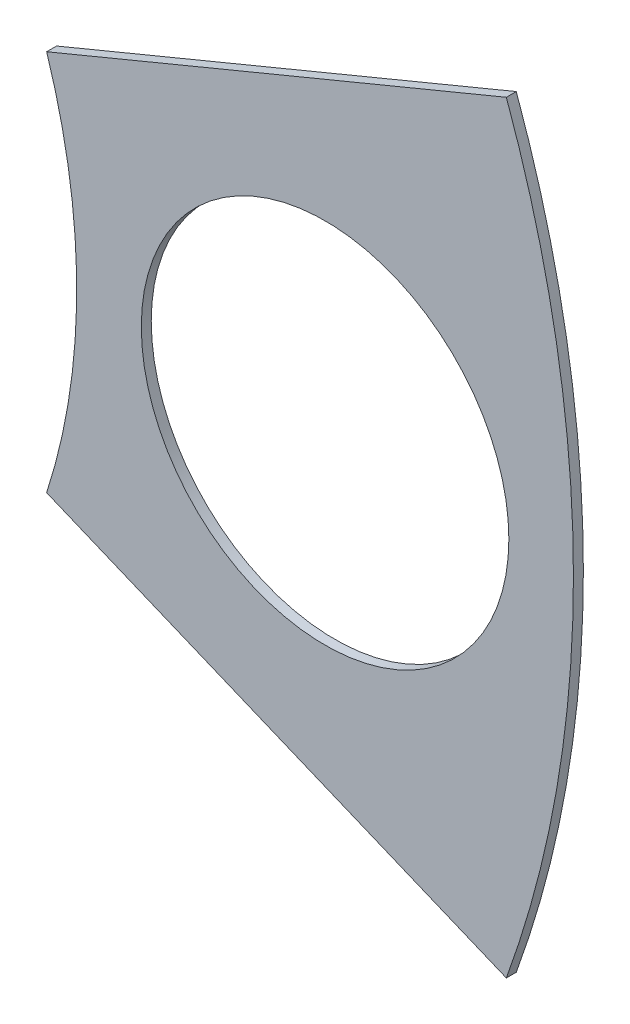
SolidWorks part; units mm, degrees
material "Copper"
ref_plane "Front Plane" through (0, 0, 0) normal (0, 0, 1) x (1, 0, 0)
ref_plane "Top Plane" through (0, 0, 0) normal (0, 1, 0) x (1, 0, 0)
ref_plane "Right Plane" through (0, 0, 0) normal (1, 0, 0) x (0, 0, -1)
sketch "Sketch4" plane through (0, 0, 0) normal (0, 0, 1) x (1, 0, 0)
  circle A0 centre (0, 0) radius 28.575
  dimension "D1" = 57.15
extrude "Boss-Extrude2" add sketch "Sketch4" along normal blind 0.254
sketch "Sketch5" plane through (0, 0, 0.254) normal (0, 0, 1) x (1, 0, 0)
  circle A0 centre (0, 0) radius 15.875
  circle A1 centre (0, 0) radius 28.575 construction
  dimension "D1" = 12.7
extrude "Cut-Extrude5" cut sketch "Sketch5" against normal through all
sketch "Sketch6" plane through (0, 0, 0.254) normal (0, 0, 1) x (1, 0, 0)
  line L0 (0, 0) -> (22.225, 0) construction
  circle A0 centre (22.225, 0) radius 4.699
  circle A1 centre (0, 0) radius 15.875 construction
  dimension "D2" = 9.398
  dimension "D1" = 6.35
extrude "Cut-Extrude6" cut sketch "Sketch6" against normal through all
sketch "Sketch8" plane through (0, 0, 0.254) normal (0, 0, 1) x (1, 0, 0)
  line L0 (0, 0) -> (26.3999, 10.9352) construction
  line L1 (0, 0) -> (26.3999, -10.9352) construction
  line L2 (15.1056, 4.8823) -> (26.8598, 9.751)
  line L3 (15.1056, -4.8823) -> (26.8598, -9.751)
  line L6 (0, 0) -> (50.4438, 0) construction
  arc A0 (26.8598, -9.751) -> (26.8598, 9.751) centre (0, 0) ccw
  arc A1 (15.1056, 4.8823) -> (15.1056, -4.8823) centre (0, 0) cw
  circle A3 centre (0, 0) radius 15.875 construction
  circle A5 centre (0, 0) radius 28.575 construction
  point P26 (0, 0)
  dimension "D3" = 22.5
  dimension "D4" = 1.27
  dimension "D5" = 15.875
  dimension "D6" = 28.575
  dimension "D1" = 1.27
  dimension "D2" = 22.5
extrude "Cut-Extrude11" cut sketch "Sketch8" against normal through all flip side to cut
